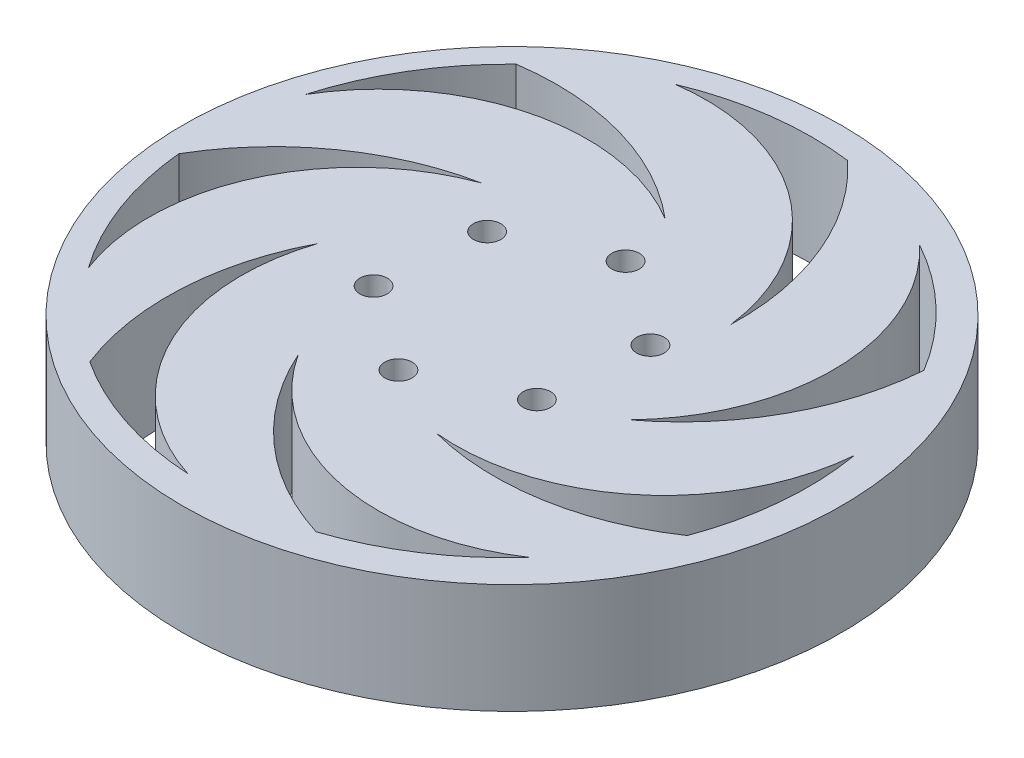
SolidWorks part; units mm, degrees
ref_plane "Front Plane" through (0, 0, 0) normal (0, 0, 1) x (1, 0, 0)
ref_plane "Top Plane" through (0, 0, 0) normal (0, 1, 0) x (1, 0, 0)
ref_plane "Right Plane" through (0, 0, 0) normal (1, 0, 0) x (0, 0, -1)
sketch "Sketch1" plane through (0, 0, 0) normal (0, 1, 0) x (1, 0, 0)
  circle A1 centre (0, 0) radius 30
  dimension "D1" = 60
extrude "Boss-Extrude1" add sketch "Sketch1" along normal blind 10 contours A1
sketch "Sketch2" plane through (0, 10, 0) normal (0, 1, 0) x (1, 0, 0)
  circle A0 centre (0, 0) radius 9.5
  circle A1 centre (-7.7539, 5.4888) radius 1.25
  circle A2 centre (0.8764, 9.4595) radius 1.25
  circle A3 centre (8.6304, 3.9707) radius 1.25
  circle A4 centre (7.7539, -5.4888) radius 1.25
  circle A5 centre (-0.8764, -9.4595) radius 1.25
  circle A6 centre (-8.6304, -3.9707) radius 1.25
  point P17 (0, 0)
  dimension "D1" = 19
  dimension "D2" = 2.5
  dimension "D3" = 6
extrude "Cut-Extrude1" cut sketch "Sketch2" against normal up to next contours A1 | A5 | A4 | A3 | A2 | A6
sketch "Sketch6" plane through (0, 10, 0) normal (0, 1, 0) x (1, 0, 0)
  line L0 (8.6304, 3.9707) -> (7.7539, -5.4888) construction
  line L2 (0, 0) -> (-27.8806, 2.5832)
  line L3 (0, 0) -> (-11.7032, 25.4369)
  line L4 (0, 0) -> (16.1774, 22.8537)
  line L5 (0, 0) -> (27.8806, -2.5832)
  line L6 (0, 0) -> (11.7032, -25.4369)
  line L7 (0, 0) -> (-16.1774, -22.8537)
  arc A0 (25.3241, -9.3644) -> (26.6135, 4.5522) centre (0, 0) ccw
  arc A1 (1.0395, -26.98) -> (19.8128, -18.3427) centre (0, 0) ccw
  arc A2 (-22.8456, -14.3902) -> (-5.9788, -26.3297) centre (0, 0) ccw
  arc A3 (-23.8851, 12.5897) -> (-25.7916, -7.987) centre (0, 0) ccw
  arc A4 (-1.0395, 26.98) -> (-19.8128, 18.3427) centre (0, 0) ccw
  arc A5 (22.8456, 14.3902) -> (5.9788, 26.3297) centre (0, 0) ccw
  circle A6 centre (0, 0) radius 14
  arc A9 (26.6135, 4.5522) -> (5.8516, -12.7185) centre (7.6845, 6.1929) cw
  arc A10 (25.3241, -9.3644) -> (5.8516, -12.7185) centre (11.8751, 10.5134) cw
  point P8 (8.1922, -0.759)
  point P16 (0, 0)
  point P18 (26.8848, -2.491)
  point P29 (0, 0)
  dimension "D2" = 27
  dimension "D5" = 28
  dimension "D8" = 24
  dimension "D9" = 15.5573
  dimension "D4" = 19
  dimension "D3" = 0
  dimension "D6" = 28
  dimension "D7" = 0
  dimension "D1" = 6
extrude "Cut-Extrude4" cut sketch "Sketch6" against normal blind 10 contours A10 A0 L5 A9 | A0 A9 L5
pattern_circular "CirPattern2" count 7 over 360 about axis through (-0.5066, 0, -0.1917) along (0, 1, 0) of "Cut-Extrude4"
